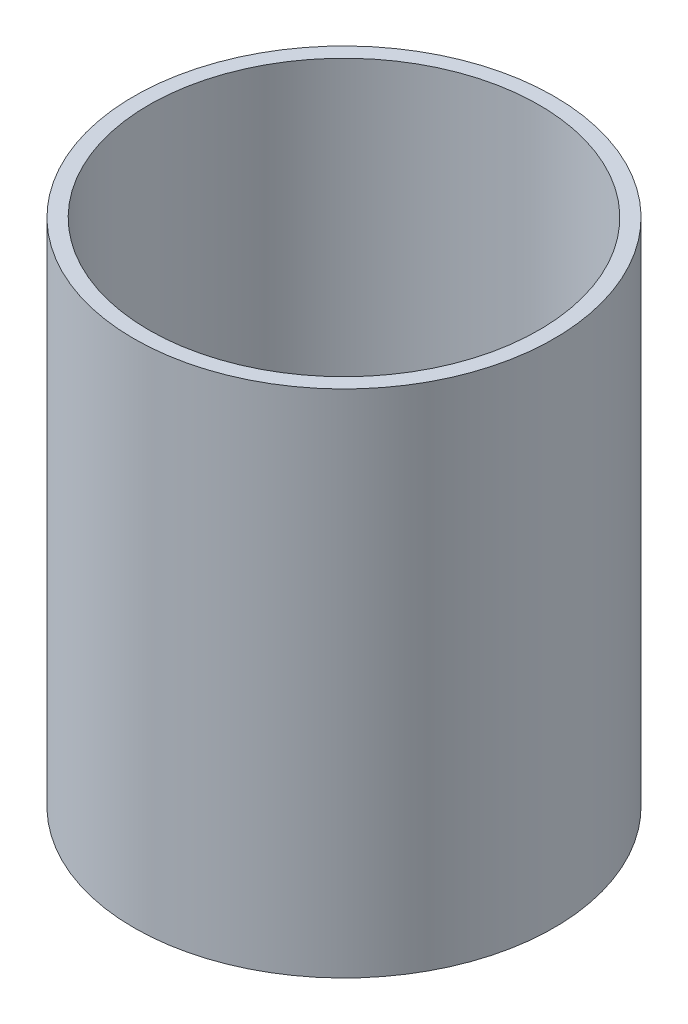
SolidWorks part; units mm, degrees
material "Corrugated Paper"
ref_plane "Front Plane" through (0, 0, 0) normal (0, 0, 1) x (1, 0, 0)
ref_plane "Top Plane" through (0, 0, 0) normal (0, 1, 0) x (1, 0, 0)
ref_plane "Right Plane" through (0, 0, 0) normal (1, 0, 0) x (0, 0, -1)
ref_axis "Axis1" through (0, 55, 0) along (0, -1, 0)
sketch "Sketch1" plane through (0, 0, 0) normal (0, 0, 1) x (1, 0, 0)
  line L1 (-44.45, 36.9791) -> (-41.275, 36.9791)
  line L2 (-44.45, 36.9791) -> (-44.45, -70.9709)
  line L3 (-44.45, -70.9709) -> (-41.275, -70.9709)
  line L4 (-41.275, 36.9791) -> (-41.275, -70.9709)
  line L5 (0, 36.9791) -> (-38.1, 36.9791) construction
  line L6 (0, -70.9709) -> (-38.1, -70.9709) construction
  dimension "D1" = 3.175
revolve "Revolve1" add sketch "Sketch1" angle 360 about axis through (0, 55, 0) along (0, -1, 0)
